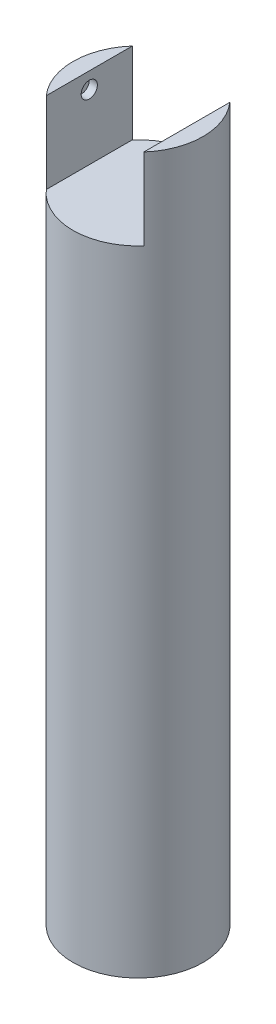
SolidWorks part; units mm, degrees
ref_plane "Front Plane" through (0, 0, 0) normal (0, 0, 1) x (1, 0, 0)
ref_plane "Top Plane" through (0, 0, 0) normal (0, 1, 0) x (1, 0, 0)
ref_plane "Right Plane" through (0, 0, 0) normal (1, 0, 0) x (0, 0, -1)
sketch "Sketch2" plane through (0, 0, 0) normal (0, 1, 0) x (1, 0, 0)
  circle A0 centre (0, 0) radius 20
  dimension "D1" = 40
extrude "Boss-Extrude1" add sketch "Sketch2" along normal blind 220
sketch "Sketch3" plane through (0, 220, 0) normal (0, 1, 0) x (1, 0, 0)
  line L1 (-15, 20.8906) -> (15, 20.8906)
  line L2 (-15, 20.8906) -> (-15, -20.8906)
  line L3 (-15, -20.8906) -> (15, -20.8906)
  line L4 (15, 20.8906) -> (15, -20.8906)
  line L5 (-15, 20.8906) -> (15, -20.8906) construction
  line L6 (-15, -20.8906) -> (15, 20.8906) construction
  point P0 (0, 0)
  dimension "D1" = 30
extrude "Cut-Extrude1" cut sketch "Sketch3" against normal blind 25
sketch "Sketch4" plane through (-15, 0, 0) normal (1, 0, 0) x (0, 0, -1)
  line L0 (-20, 0) -> (20, 0) construction
  circle A0 centre (0, 215) radius 2.5
  dimension "D1" = 5
  dimension "D2" = 215
extrude "Cut-Extrude2" cut sketch "Sketch4" against normal blind 2.5 contours A0
mirror "Mirror1" about plane through (0, 0, 0) normal (1, 0, 0) of "Cut-Extrude2"
